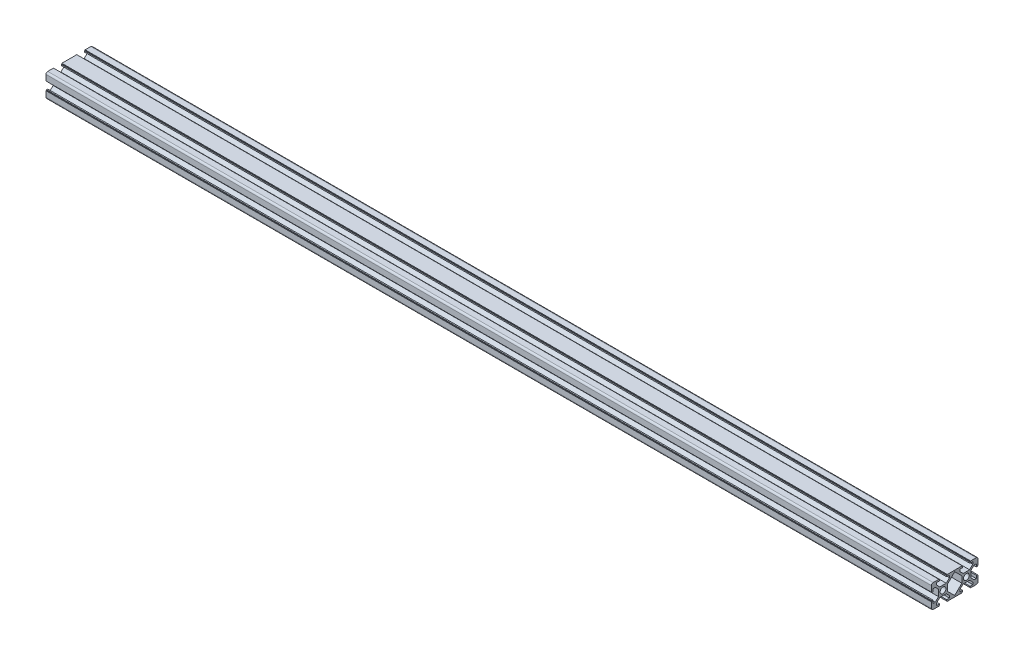
SolidWorks part; units mm, degrees
ref_plane "前视基准面" through (0, 0, 0) normal (0, 0, 1) x (1, 0, 0)
ref_plane "上视基准面" through (0, 0, 0) normal (0, 1, 0) x (1, 0, 0)
ref_plane "右视基准面" through (0, 0, 0) normal (1, 0, 0) x (0, 0, -1)
sketch "草图1" plane through (0, 0, 0) normal (0, 0, 1) x (1, 0, 0)
  line L0 (0, 0) -> (760, 0)
other "铝型材 20 X 40 X T1.5(1)"
ref_plane "基准面5" through (0, 0, 0) normal (1, 0, 0) x (0, 1, 0)
sketch "Sketch1" plane through (0, 0, 0) normal (1, 0, 0) x (0, 1, 0)
  line L0 (-3.6, 10) -> (-3.6, 9.5)
  line L1 (-3.6, 9.5) -> (-3.1, 9.5)
  line L2 (-3.1, 9.5) -> (-3.1, 8.5)
  line L3 (-3.1, 8.5) -> (-5.5, 8.5)
  line L4 (8.85, -10) -> (2.75, -3.9)
  line L5 (-10, -16.4) -> (-10, -3.6)
  line L6 (8.5, 10) -> (3.6, 10)
  line L7 (10, 8.5) -> (10, 3.6)
  line L8 (0, 14.8756) -> (0, 0) construction
  line L9 (0, 0) -> (10, 0) construction
  line L10 (-5.5, 8.5) -> (-5.5, 6.65)
  line L11 (-5.5, 6.65) -> (-2.75, 3.9)
  line L12 (-2.75, 3.9) -> (2.75, 3.9)
  line L13 (5.5, 6.65) -> (2.75, 3.9)
  line L14 (5.5, 8.5) -> (5.5, 6.65)
  line L15 (3.1, 8.5) -> (5.5, 8.5)
  line L16 (3.1, 9.5) -> (3.1, 8.5)
  line L17 (3.6, 9.5) -> (3.1, 9.5)
  line L18 (3.6, 10) -> (3.6, 9.5)
  line L19 (-3.6, 10) -> (-8.5, 10)
  line L20 (10, 3.6) -> (9.5, 3.6)
  line L21 (9.5, 3.6) -> (9.5, 3.1)
  line L22 (9.5, 3.1) -> (8.5, 3.1)
  line L23 (8.5, 3.1) -> (8.5, 5.5)
  line L24 (8.5, 5.5) -> (6.65, 5.5)
  line L25 (6.65, 5.5) -> (3.9, 2.75)
  line L26 (3.9, 2.75) -> (3.9, -2.75)
  line L27 (6.65, -5.5) -> (3.9, -2.75)
  line L28 (8.5, -5.5) -> (6.65, -5.5)
  line L29 (8.5, -3.1) -> (8.5, -5.5)
  line L30 (9.5, -3.1) -> (8.5, -3.1)
  line L31 (9.5, -3.6) -> (9.5, -3.1)
  line L32 (10, -3.6) -> (9.5, -3.6)
  line L33 (8.85, -10) -> (2.75, -16.1)
  line L34 (-8.85, -10) -> (-2.75, -16.1)
  line L35 (-8.85, -10) -> (-2.75, -3.9)
  line L39 (2.75, -3.9) -> (-2.75, -3.9)
  line L46 (-10, -3.6) -> (-9.5, -3.6)
  line L47 (-9.5, -3.6) -> (-9.5, -3.1)
  line L48 (-9.5, -3.1) -> (-8.5, -3.1)
  line L49 (-8.5, -3.1) -> (-8.5, -5.5)
  line L50 (-8.5, -5.5) -> (-6.65, -5.5)
  line L51 (-6.65, -5.5) -> (-3.9, -2.75)
  line L52 (-3.9, -2.75) -> (-3.9, 2.75)
  line L53 (-6.65, 5.5) -> (-3.9, 2.75)
  line L54 (-8.5, 5.5) -> (-6.65, 5.5)
  line L55 (-8.5, 3.1) -> (-8.5, 5.5)
  line L56 (-9.5, 3.1) -> (-8.5, 3.1)
  line L57 (-9.5, 3.6) -> (-9.5, 3.1)
  line L58 (-10, 3.6) -> (-9.5, 3.6)
  line L60 (-10, 3.6) -> (-10, 8.5)
  line L61 (10, -3.6) -> (10, -16.4)
  line L66 (-8.5, -30) -> (-3.6, -30)
  line L67 (-10, -28.5) -> (-10, -23.6)
  line L72 (-2.75, -16.1) -> (2.75, -16.1)
  line L80 (10, -16.4) -> (9.5, -16.4)
  line L81 (9.5, -16.4) -> (9.5, -16.9)
  line L82 (9.5, -16.9) -> (8.5, -16.9)
  line L83 (8.5, -16.9) -> (8.5, -14.5)
  line L84 (8.5, -14.5) -> (6.65, -14.5)
  line L85 (6.65, -14.5) -> (3.9, -17.25)
  line L86 (3.9, -17.25) -> (3.9, -22.75)
  line L87 (6.65, -25.5) -> (3.9, -22.75)
  line L88 (8.5, -25.5) -> (6.65, -25.5)
  line L89 (8.5, -23.1) -> (8.5, -25.5)
  line L90 (9.5, -23.1) -> (8.5, -23.1)
  line L91 (9.5, -23.6) -> (9.5, -23.1)
  line L92 (10, -23.6) -> (9.5, -23.6)
  line L93 (3.6, -30) -> (3.6, -29.5)
  line L94 (3.6, -29.5) -> (3.1, -29.5)
  line L95 (3.1, -29.5) -> (3.1, -28.5)
  line L96 (3.1, -28.5) -> (5.5, -28.5)
  line L97 (5.5, -28.5) -> (5.5, -26.65)
  line L98 (5.5, -26.65) -> (2.75, -23.9)
  line L99 (2.75, -23.9) -> (-2.75, -23.9)
  line L100 (-5.5, -26.65) -> (-2.75, -23.9)
  line L101 (-5.5, -28.5) -> (-5.5, -26.65)
  line L102 (-3.1, -28.5) -> (-5.5, -28.5)
  line L103 (-3.1, -29.5) -> (-3.1, -28.5)
  line L104 (-3.6, -29.5) -> (-3.1, -29.5)
  line L105 (-3.6, -30) -> (-3.6, -29.5)
  line L106 (-10, -23.6) -> (-9.5, -23.6)
  line L107 (-9.5, -23.6) -> (-9.5, -23.1)
  line L108 (-9.5, -23.1) -> (-8.5, -23.1)
  line L109 (-8.5, -23.1) -> (-8.5, -25.5)
  line L110 (-8.5, -25.5) -> (-6.65, -25.5)
  line L111 (-6.65, -25.5) -> (-3.9, -22.75)
  line L112 (-3.9, -22.75) -> (-3.9, -17.25)
  line L113 (-6.65, -14.5) -> (-3.9, -17.25)
  line L114 (-8.5, -14.5) -> (-6.65, -14.5)
  line L115 (-8.5, -16.9) -> (-8.5, -14.5)
  line L116 (-9.5, -16.9) -> (-8.5, -16.9)
  line L117 (-9.5, -16.4) -> (-9.5, -16.9)
  line L118 (-10, -16.4) -> (-9.5, -16.4)
  line L119 (3.6, -30) -> (8.5, -30)
  line L121 (10, -23.6) -> (10, -28.5)
  line L122 (0, -20) -> (10, -20) construction
  line L125 (3.6, -10) -> (3.6, -9.5) [skipped]
  line L127 (3.6, -9.5) -> (3.1, -9.5) [skipped]
  line L129 (3.1, -9.5) -> (3.1, -8.5) [skipped]
  line L131 (3.1, -8.5) -> (5.5, -8.5) [skipped]
  line L133 (-3.1, -8.5) -> (-5.5, -8.5) [skipped]
  line L135 (-3.1, -9.5) -> (-3.1, -8.5) [skipped]
  line L137 (-3.6, -9.5) -> (-3.1, -9.5) [skipped]
  line L139 (-3.6, -10) -> (-3.6, -9.5) [skipped]
  line L141 (-3.6, -10) -> (-3.6, -10.5) [skipped]
  line L142 (-3.6, -10.5) -> (-3.1, -10.5) [skipped]
  line L143 (-3.1, -10.5) -> (-3.1, -11.5) [skipped]
  line L144 (-3.1, -11.5) -> (-5.5, -11.5) [skipped]
  line L145 (8.5, -10) -> (3.6, -10) [skipped]
  line L146 (3.1, -11.5) -> (5.5, -11.5) [skipped]
  line L147 (3.1, -10.5) -> (3.1, -11.5) [skipped]
  line L148 (3.6, -10.5) -> (3.1, -10.5) [skipped]
  line L149 (3.6, -10) -> (3.6, -10.5) [skipped]
  line L150 (-3.6, -10) -> (-8.5, -10) [skipped]
  line L151 (-10, -16.4) -> (-10, -11.5) [skipped]
  line L152 (10, -11.5) -> (10, -16.4) [skipped]
  line L154 (-5.5, -8.5) -> (-5.5, -6.65) [skipped]
  line L156 (5.5, -8.5) -> (5.5, -6.65) [skipped]
  line L157 (5.5, -11.5) -> (5.5, -13.35) [skipped]
  line L158 (-5.5, -11.5) -> (-5.5, -13.35) [skipped]
  line L160 (-12.2446, -13.3946) -> (-10, -11.15) [skipped]
  line L161 (13.644, -5.206) -> (10, -8.85) [skipped]
  line L163 (12.1963, -13.3463) -> (10, -11.15) [skipped]
  line L164 (-11.1344, -7.7156) -> (-10, -8.85) [skipped]
  circle A0 centre (0, 0) radius 2.5
  arc A1 (-10, 8.5) -> (-8.5, 10) centre (-8.5, 8.5) cw
  arc A2 (10, 8.5) -> (8.5, 10) centre (8.5, 8.5) ccw
  arc A3 (10, -28.5) -> (8.5, -30) centre (8.5, -28.5) cw
  arc A4 (-10, -28.5) -> (-8.5, -30) centre (-8.5, -28.5) ccw
  circle A5 centre (0, -20) radius 2.5
  arc A12 (-10, -11.5) -> (-8.5, -10) centre (-8.5, -11.5) cw [skipped]
  arc A13 (10, -11.5) -> (8.5, -10) centre (8.5, -11.5) ccw [skipped]
  point P0 (-10, 0)
  point P1 (10, 0)
  point P2 (0, 10)
  point P4 (0, 0)
  point P5 (0, -10)
  point P6 (-10, -10)
  point P7 (10, 10)
  point P8 (-10, 10)
  point P12 (-10, -10)
  point P13 (10, -10)
  point P15 (0, -10)
  point P16 (10, -10)
  point P36 (-10, 10)
  point P39 (10, 10)
  point P43 (-10, -20)
  point P44 (10, -20)
  point P62 (0, 0)
  point P88 (0, -30)
  point P89 (0, -20)
  point P90 (-10, -30)
  point P91 (10, -30)
  dimension "D1" = 11
  dimension "D2" = 20
  dimension "D3" = 6.2
  dimension "D4" = 7.2
  dimension "D5" = 6.1
  dimension "D6" = 5
  dimension "D7" = 1.5
  dimension "D8" = 45
  dimension "D14" = 20
  dimension "D15" = 1.5
  dimension "D9" = 0.5
  dimension "D10" = 1
  dimension "D11" = 5.5
  dimension "D12" = 10
  dimension "D13" = 40
  dimension "D16" = 45
  dimension "D17" = 45
  dimension "D18" = 45
  dimension "D19" = 6.2
